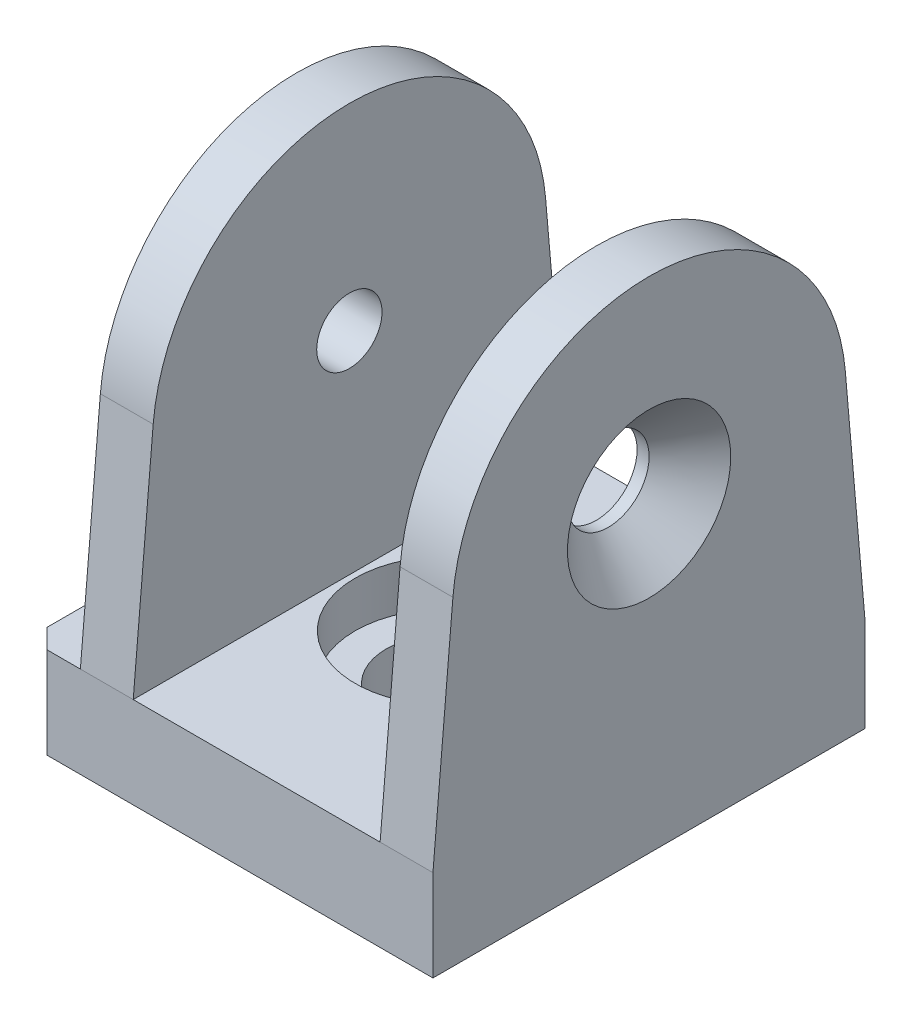
SolidWorks part; units mm, degrees
material "Алюминиевый сплав"
ref_plane "Спереди" through (0, 0, 0) normal (0, 0, 1) x (1, 0, 0)
ref_plane "Сверху" through (0, 0, 0) normal (0, 1, 0) x (1, 0, 0)
ref_plane "Справа" through (0, 0, 0) normal (1, 0, 0) x (0, 0, -1)
sketch "Эскиз1" plane through (0, 0, 0) normal (0, 1, 0) x (1, 0, 0)
  line L1 (21.1, -22.5) -> (-21.1, -22.5)
  line L2 (21.1, -22.5) -> (21.1, 22.5)
  line L3 (21.1, 22.5) -> (-21.1, 22.5)
  line L4 (-21.1, -22.5) -> (-21.1, 22.5)
  line L5 (21.1, -22.5) -> (-21.1, 22.5) construction
  line L6 (21.1, 22.5) -> (-21.1, -22.5) construction
  point P0 (0, 0)
  dimension "D1" = 42.2
  dimension "D2" = 45
extrude "Бобышка-Вытянуть1" add sketch "Эскиз1" along normal blind 9.5
sketch "Эскиз2" plane through (0, 0, 0) normal (0, 0, 1) x (1, 0, 0)
  line L1 (-21.1, 0) -> (21.1, 0) construction
  line L2 (-6.25, 0) -> (-6.25, 4.75)
  line L3 (-6.25, 4.75) -> (-9.5, 4.75)
  line L4 (-9.5, 4.75) -> (-9.5, 9.5)
  line L5 (-21.1, 9.5) -> (21.1, 9.5) construction
  line L7 (0, 9.5) -> (0, 0) construction
  line L11 (-21.1, 9.5) -> (-21.1, 0) construction
  line L12 (-9.5, 9.5) -> (0, 9.5)
  line L13 (0, 0) -> (-6.25, 0)
  line L14 (0, 0) -> (0, 9.5)
  point P17 (-21.1, 4.75)
  dimension "D1" = 12.5
  dimension "D2" = 19
revolve "Вырез-Повернуть1" cut sketch "Эскиз2" angle 360 about L7
sketch "Эскиз3" plane through (21.1, 0, 0) normal (1, 0, 0) x (0, 0, -1)
  line L0 (-22.5, 9.5) -> (-20.4222, 33.2841)
  line L1 (20.4222, 33.2841) -> (22.5, 9.5)
  line L2 (22.5, 9.5) -> (-22.5, 9.5)
  line L3 (-22.5, 0) -> (22.5, 0) construction
  arc A0 (-20.4222, 33.2841) -> (20.4222, 33.2841) centre (0, 31.5) cw
  dimension "D1" = 52
  dimension "D2" = 22
extrude "Бобышка-Вытянуть2" add sketch "Эскиз3" against normal blind 36.7
sketch "Эскиз4" plane through (0, 0, 0) normal (0, 0, 1) x (1, 0, 0)
  line L0 (-15.6, 9.5) -> (21.1, 9.5) construction
  line L1 (15.6, 9.5) -> (-10.1, 9.5)
  line L2 (15.6, 9.5) -> (15.6, 52)
  line L3 (15.6, 52) -> (-10.1, 52)
  line L4 (-10.1, 9.5) -> (-10.1, 52)
  line L5 (21.1, 52) -> (-15.6, 52) construction
  line L6 (15.6, 30.75) -> (21.1, 30.75) construction
  line L7 (21.1, 33.2841) -> (21.1, 9.5) construction
  line L8 (-10.1, 30.75) -> (-15.6, 30.75) construction
  line L9 (-15.6, 33.2841) -> (-15.6, 9.5) construction
  dimension "D1" = 5.5
extrude "Вырез-Вытянуть1" cut sketch "Эскиз4" against normal through all and the other way through all
chamfer "Фаска1" distance 2 angle 45 2 edges at (-21.1, 4.75, -22.5) (-21.1, 4.75, 22.5)
hole_wizard "Зенковка для винта с полупотайной головкой M81" positions "Эскиз8" profile "Эскиз10" countersink size "M8" standard "ISO" end condition up to next
sketch "Эскиз8" plane through (21.1, 0, 0) normal (1, 0, 0) x (0, 0, -1)
  point P0 (0, 31.5)
sketch "Эскиз10" plane through (21.1, 31.5, 0) normal (0, 1, 0) x (0, 0, -1)
  line L0 (0, 0) -> (0, 5.5)
  line L1 (0, 5.5) -> (4.25, 5.5)
  line L2 (4.25, 5.5) -> (4.25, 4.25)
  line L3 (4.25, 4.25) -> (8.5, 0)
  line L5 (8.5, 0) -> (0, 0)
  line L6 (-4.25, 4.25) -> (-8.5, 0) construction
  line L11 (0, -6.35) -> (0, 107.95) construction
  dimension "Диаметр сквозного отверстия" = 8.5
  dimension "Глубина сквозного отверстия" = 5.5
  dimension "Диаметр передней зенковки" = 17
  dimension "Угол передней зенковки" = 90
hole_wizard "Отверстие обработанное метчиком M81" positions "Эскиз11" profile "Эскиз13" tap size "M8" standard "ISO" end condition up to next
sketch "Эскиз11" plane through (-15.6, 0, 0) normal (-1, 0, 0) x (0, 0, 1)
  point P0 (0, 31.5)
sketch "Эскиз13" plane through (-15.6, 31.5, 0) normal (0, 1, 0) x (0, 0, 1)
  line L0 (0, 0) -> (0, 5.5)
  line L1 (0, 5.5) -> (3.4, 5.5)
  line L2 (3.4, 5.5) -> (3.4, 0)
  line L5 (3.4, 0) -> (0, 0)
  line L11 (0, -6.35) -> (0, 107.95) construction
  dimension "Диаметр проходного сверла" = 6.8
  dimension "Глубина проходного сверла" = 5.5
cosmetic thread "Отверстие резьбы1" parameters "D2"=8
